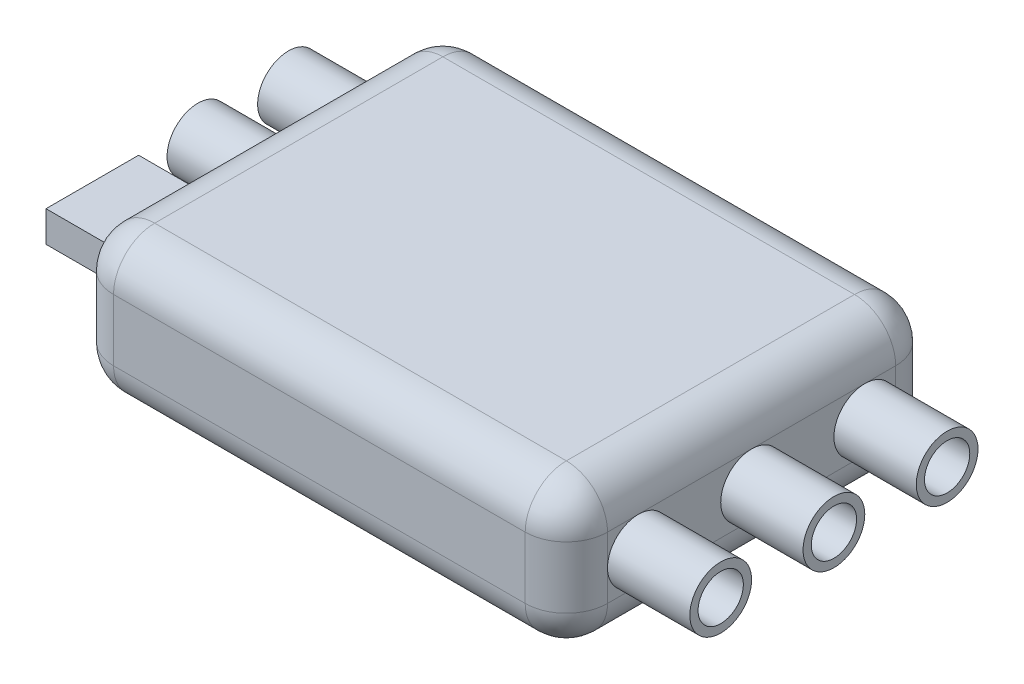
SolidWorks part; units mm, degrees
ref_plane "Front Plane" through (0, 0, 0) normal (0, 0, 1) x (1, 0, 0)
ref_plane "Top Plane" through (0, 0, 0) normal (0, 1, 0) x (1, 0, 0)
ref_plane "Right Plane" through (0, 0, 0) normal (1, 0, 0) x (0, 0, -1)
sketch "Sketch1" plane through (0, 0, 0) normal (0, 1, 0) x (1, 0, 0)
  line L5 (10, -9) -> (-10, -9)
  line L6 (12, -7) -> (12, 7)
  line L7 (10, 9) -> (-10, 9)
  line L8 (-12, -7) -> (-12, 7)
  line L9 (12, -9) -> (-12, 9) construction
  line L10 (12, 9) -> (-12, -9) construction
  arc A0 (-10, -9) -> (-12, -7) centre (-10, -7) cw
  arc A1 (12, 7) -> (10, 9) centre (10, 7) ccw
  arc A2 (10, -9) -> (12, -7) centre (10, -7) ccw
  arc A3 (-10, 9) -> (-12, 7) centre (-10, 7) ccw
  point P0 (0, 0)
  dimension "D3" = 2
  dimension "D1" = 24
  dimension "D2" = 18
extrude "Boss-Extrude1" add sketch "Sketch1" along normal blind 7
fillet "Fillet1" radius 2 16 edges at (0, 0, 9) (11.4142, 0, 8.4142) (12, 0, 0) (11.4142, 0, -8.4142) (0, 0, -9) (-11.4142, 0, -8.4142) (-12, 0, 0) (-11.4142, 0, 8.4142) (-12, 7, 0) (-11.4142, 7, -8.4142) (0, 7, -9) (11.4142, 7, -8.4142) (12, 7, 0) (11.4142, 7, 8.4142) (0, 7, 9) (-11.4142, 7, 8.4142)
sketch "Sketch2" plane through (12, 0, 0) normal (1, 0, 0) x (0, 0, -1)
  line L0 (-7, 3.5) -> (7, 3.5) construction
  line L1 (-7, 5) -> (-7, 2) construction
  line L2 (7, 5) -> (7, 2) construction
  circle A0 centre (0, 3.5) radius 1.5
  circle A1 centre (0, 3.5) radius 1.1
  circle A2 centre (-5.5, 3.5) radius 1.5
  circle A3 centre (5.5, 3.5) radius 1.5
  circle A4 centre (5.5, 3.5) radius 1.1
  circle A5 centre (-5.5, 3.5) radius 1.1
  dimension "D1" = 3
  dimension "D2" = 0.4
extrude "Boss-Extrude2" add sketch "Sketch2" along normal blind 4
sketch "Sketch3" plane through (-12, 0, 0) normal (-1, 0, 0) x (0, 0, 1)
  line L0 (-7, 3.5) -> (7, 3.5) construction
  line L1 (-7, 5) -> (-7, 2) construction
  line L2 (7, 5) -> (7, 2) construction
  line L4 (6.2813, 4.25) -> (1.7813, 4.25)
  line L5 (6.2813, 4.25) -> (6.2813, 2.75)
  line L6 (6.2813, 2.75) -> (1.7813, 2.75)
  line L7 (1.7813, 4.25) -> (1.7813, 2.75)
  circle A0 centre (-5.5, 3.5) radius 1.5
  circle A1 centre (-1.1, 3.5) radius 1.5
  circle A2 centre (-1.1, 3.5) radius 1.1
  circle A3 centre (-5.5, 3.5) radius 1.1
  dimension "D3" = 3
  dimension "D4" = 0.4
  dimension "D1" = 4.5
  dimension "D2" = 1.5
  dimension "D5" = 4.4
extrude "Boss-Extrude3" add sketch "Sketch3" along normal blind 4
